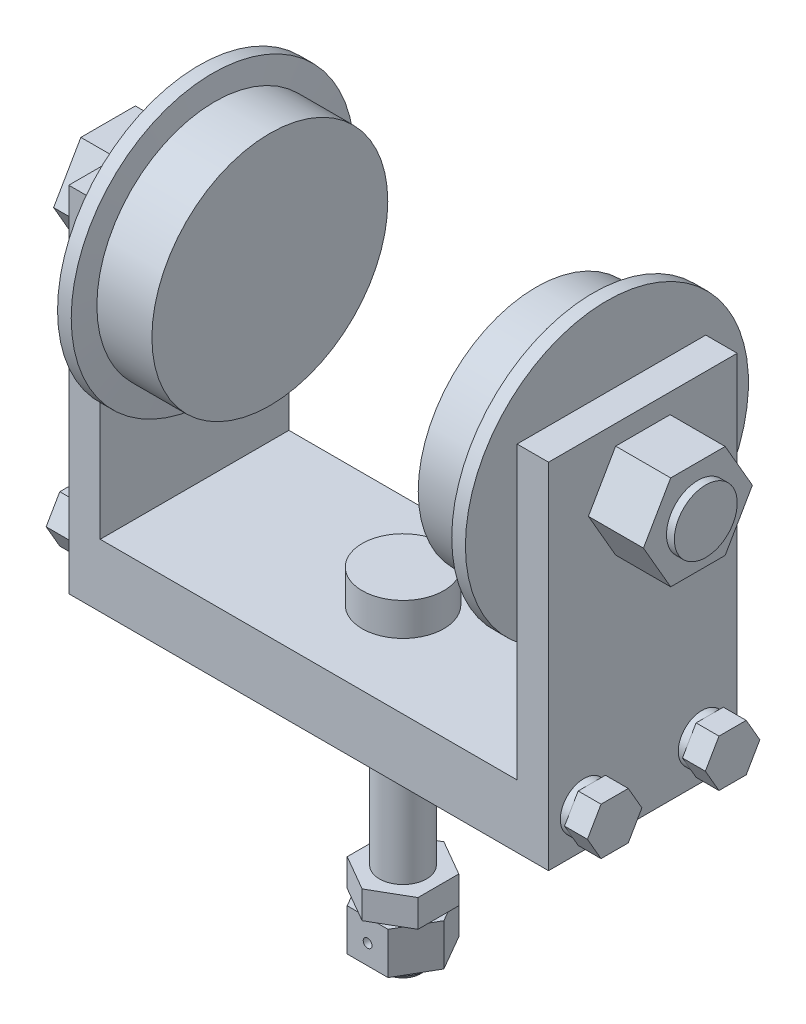
SolidWorks part; units mm, degrees
ref_plane "Front" through (0, 0, 0) normal (0, 0, 1) x (1, 0, 0)
ref_plane "Top" through (0, 0, 0) normal (0, 1, 0) x (1, 0, 0)
ref_plane "Right" through (0, 0, 0) normal (1, 0, 0) x (0, 0, -1)
ref_plane "Z PLANE" through (0, 0, 0) normal (0, 0, 1) x (1, 0, 0)
ref_plane "YOKE BOTTOM" through (0, 0, 0) normal (0, 1, 0) x (-1, 0, 0)
ref_plane "X PLANE" through (0, 0, 0) normal (1, 0, 0) x (0, 0, -1)
sketch "YOKE CROSS SECTION" plane through (0, 0, 0) normal (1, 0, 0) x (0, 0, -1)
  line L0 (0, 0) -> (0, 57.0916) construction
  line L1 (0, 72.125) -> (0, -72.125) construction
  line L2 (-38.1, 0) -> (38.1, 0)
  line L3 (69.1602, 0) -> (-69.1602, 0) construction
  line L4 (38.1, 0) -> (38.1, 25.4)
  line L5 (-38.1, 0) -> (-38.1, 25.4)
  line L6 (38.1, 25.4) -> (-38.1, 25.4)
  point P12 (0, 25.4)
  dimension "D1" = 25.4
  dimension "D2" = 76.2
ref_plane "1/2 YOKE LENGTH (A)" through (84.164, 0, 0) normal (1, 0, 0) x (0, 0, -1)
extrude "YOKE" add sketch "YOKE CROSS SECTION" along normal up to surface (84.164 mm away) up to plane "1/2 YOKE LENGTH (A)"
sketch "SIDEPLATE PROFILE" plane through (84.164, 0, 0) normal (1, 0, 0) x (0, 0, -1)
  line L0 (0, 0) -> (0, 74.7424) construction
  line L1 (0, 72.125) -> (0, -72.125) construction
  line L2 (-38.1, 0) -> (38.1, 0)
  line L3 (38.1, 0) -> (38.1, 142.875)
  line L4 (-38.1, 0) -> (-38.1, 142.875)
  line L5 (38.1, 142.875) -> (-38.1, 142.875)
  point P11 (0, 142.875)
  dimension "D1" = 142.875
ref_plane "WHEEL HEIGHT" through (0, 115.8875, 0) normal (0, 1, 0) x (-1, 0, 0)
ref_plane "SCREW LOCATION X" through (0, 0, 23.8125) normal (0, 0, 1) x (1, 0, 0)
ref_plane "SCREW LOCATION Y" through (0, 15.5632, 0) normal (0, 1, 0) x (-1, 0, 0)
extrude "SIDEPLATE" add sketch "SIDEPLATE PROFILE" along normal blind 12.7
sketch "WHEEL PIN NUT PROFILE" plane through (96.864, 0, 0) normal (1, 0, 0) x (0, 0, -1)
  line L0 (0, 72.125) -> (0, -72.125) construction
  line L1 (21.997, 115.8875) -> (10.9985, 134.9375)
  line L2 (10.9985, 134.9375) -> (-10.9985, 134.9375)
  line L3 (-10.9985, 134.9375) -> (-21.997, 115.8875)
  line L4 (-21.997, 115.8875) -> (-10.9985, 96.8375)
  line L5 (-10.9985, 96.8375) -> (10.9985, 96.8375)
  line L6 (10.9985, 96.8375) -> (21.997, 115.8875)
  line L7 (69.1602, 115.8875) -> (-69.1602, 115.8875) construction
  circle A0 centre (0, 115.8875) radius 19.05 construction
  dimension "D1" = 38.1
extrude "WHEEL PIN NUT" add sketch "WHEEL PIN NUT PROFILE" along normal blind 22.225
sketch "WHEEL PIN PROJECTION PROFILE" plane through (119.089, 0, 0) normal (1, 0, 0) x (0, 0, -1)
  line L0 (0, 72.125) -> (0, -72.125) construction
  line L1 (69.1602, 115.8875) -> (-69.1602, 115.8875) construction
  circle A0 centre (0, 115.8875) radius 12.7
  dimension "D1" = 25.4
extrude "WHEEL PIN PROJECTION" add sketch "WHEEL PIN PROJECTION PROFILE" along normal blind 3.175
sketch "LOCKNUTS PROFILE" plane through (96.864, 0, 0) normal (1, 0, 0) x (0, 0, -1)
  line L0 (-23.8125, 84.8167) -> (-23.8125, -84.8167) construction
  line L1 (50, 15.5632) -> (-50, 15.5632) construction
  circle A0 centre (-23.8125, 15.5632) radius 9.525
  dimension "D1" = 19.05
extrude "LOCKNUTS" add sketch "LOCKNUTS PROFILE" along normal blind 3.175
sketch "SCREWS PROFILE" plane through (100.039, 0, 0) normal (1, 0, 0) x (0, 0, -1)
  line L0 (50, 15.5632) -> (-50, 15.5632) construction
  line L1 (-12.814, 15.5632) -> (-18.3132, 25.0882)
  line L2 (-18.3132, 25.0882) -> (-29.3118, 25.0882)
  line L3 (-29.3118, 25.0882) -> (-34.811, 15.5632)
  line L4 (-34.811, 15.5632) -> (-29.3118, 6.0382)
  line L5 (-29.3118, 6.0382) -> (-18.3132, 6.0382)
  line L6 (-18.3132, 6.0382) -> (-12.814, 15.5632)
  line L7 (-23.8125, 84.8167) -> (-23.8125, -84.8167) construction
  circle A0 centre (-23.8125, 15.5632) radius 9.525 construction
  dimension "D1" = 19.05
extrude "SCREWS" add sketch "SCREWS PROFILE" along normal blind 9.2456
sketch "PROFILE" plane through (0, 25.4, 0) normal (0, 1, 0) x (-1, 0, 0)
  line L0 (72.125, 0) -> (-72.125, 0) construction
  line L1 (0, 83.2389) -> (0, -83.2389) construction
  circle A0 centre (0, 0) radius 16.4973
  dimension "D1" = 32.9946
extrude "KING BOLT HEAD" add sketch "PROFILE" along normal blind 13.3096
mirror "Mirror1" about plane through (0, 0, 0) normal (0, 0, 1) of "SCREWS", "LOCKNUTS"
mirror "Mirror5" about plane through (0, 0, 0) normal (1, 0, 0) of bodies 112
ref_plane "TOP OF NUT" through (0, -65.5896, 0) normal (0, 1, 0) x (-1, 0, 0)
sketch "DIA." plane through (0, 0, 0) normal (0, -1, 0) x (1, 0, 0)
  line L0 (72.125, 0) -> (-72.125, 0) construction
  line L1 (0, -83.2389) -> (0, 83.2389) construction
  circle A0 centre (0, 0) radius 9.525
  dimension "D1" = 19.05
extrude "KING BOLT" add sketch "DIA." along normal up to surface (65.5896 mm away) up to plane "TOP OF NUT"
sketch "KING BOLT JAN NUT PROFILE" plane through (0, -65.5896, 0) normal (0, -1, 0) x (1, 0, 0)
  line L0 (72.125, 0) -> (-72.125, 0) construction
  line L1 (0, -16.4978) -> (14.2875, -8.2489)
  line L2 (14.2875, -8.2489) -> (14.2875, 8.2489)
  line L3 (14.2875, 8.2489) -> (0, 16.4978)
  line L4 (0, 16.4978) -> (-14.2875, 8.2489)
  line L5 (-14.2875, 8.2489) -> (-14.2875, -8.2489)
  line L6 (-14.2875, -8.2489) -> (0, -16.4978)
  line L7 (0, -83.2389) -> (0, 83.2389) construction
  circle A0 centre (0, 0) radius 14.2875 construction
  dimension "D1" = 28.575
extrude "KING BOLT JAM NUT" add sketch "KING BOLT JAN NUT PROFILE" along normal blind 11.1125
sketch "KING BOLT NUT PROFILE" plane through (0, -76.7021, 0) normal (0, -1, 0) x (1, 0, 0)
  line L1 (16.4978, 0) -> (8.2489, 14.2875)
  line L2 (8.2489, 14.2875) -> (-8.2489, 14.2875)
  line L3 (-8.2489, 14.2875) -> (-16.4978, 0)
  line L4 (-16.4978, 0) -> (-8.2489, -14.2875)
  line L5 (-8.2489, -14.2875) -> (8.2489, -14.2875)
  line L6 (8.2489, -14.2875) -> (16.4978, 0)
  line L10 (0, -83.2389) -> (0, 83.2389) construction
  line L11 (72.125, 0) -> (-72.125, 0) construction
  circle A0 centre (0, 0) radius 14.2875 construction
  dimension "D1" = 28.575
extrude "KING BOLT NUT" add sketch "KING BOLT NUT PROFILE" along normal blind 16.891
sketch "Sketch5" plane through (0, -93.5931, 0) normal (0, -1, 0) x (1, 0, 0)
  circle A0 centre (0, 0) radius 9.525 construction
  circle A1 centre (0, 0) radius 9.525
extrude "EXTENDED KING BOLT" add sketch "Sketch5" along normal blind 6.35
chamfer "Chamfer1" distance 2.3812 angle 45 1 edges at (0, -99.9431, -9.525)
ref_plane "MOUNTING REF PLANE" through (0, -34.925, 0) normal (0, 1, 0) x (-1, 0, 0)
sketch "Sketch7" plane through (0, 0, 0) normal (0, 0, 1) x (1, 0, 0)
  line L0 (53.7722, 163.5125) -> (53.7722, 115.8875)
  line L1 (84.164, 115.8875) -> (84.164, 131.7625)
  line L2 (53.7722, 115.8875) -> (84.164, 115.8875)
  line L3 (82.3472, 131.7625) -> (82.3472, 173.0375)
  line L4 (84.164, 131.7625) -> (82.3472, 131.7625)
  line L5 (76.8306, 173.0375) -> (75.9972, 163.5125)
  line L6 (82.3472, 173.0375) -> (76.8306, 173.0375)
  line L7 (69.1602, 115.8875) -> (-69.1602, 115.8875) construction
  line L8 (84.164, 142.875) -> (84.164, 25.4) construction
  line L9 (75.9972, 163.5125) -> (53.7722, 163.5125)
  dimension "D1" = 47.625
  dimension "D2" = 30.3917
  dimension "D6" = 1.8167
  dimension "D3" = 8.1667
  dimension "D7" = 5.5167
  dimension "D8" = 57.15
  dimension "D9" = 15.875
revolve "WHEEL" add sketch "Sketch7" angle 360 about L2
mirror "Mirror6" about plane through (0, 0, 0) normal (1, 0, 0) of "WHEEL"
sketch "Sketch8" plane through (0, 0, 14.2875) normal (0, 0, 1) x (1, 0, 0)
  line L0 (0, -83.2389) -> (0, 83.2389) construction
  line L1 (16.4978, -93.5931) -> (8.2489, -93.5931) construction
  circle A0 centre (0, -85.6556) radius 1.778
  dimension "D1" = 3.556
  dimension "D2" = 7.9375
extrude "COTTER PIN HOLE" cut sketch "Sketch8" against normal up to next
sketch "Sketch9" plane through (0, 0, 0) normal (0, -1, 0) x (1, 0, 0)
  circle A0 centre (0, 0) radius 25.4
  circle A1 centre (0, 0) radius 30.1625
  dimension "D1" = 50.8
  dimension "D2" = 60.325
extrude "SPACER" [suppressed] add sketch "Sketch9" along normal blind 12.7
ref_plane "TREAD OF TRACK" through (0, 68.2625, 0) normal (0, 1, 0) x (-1, 0, 0)
